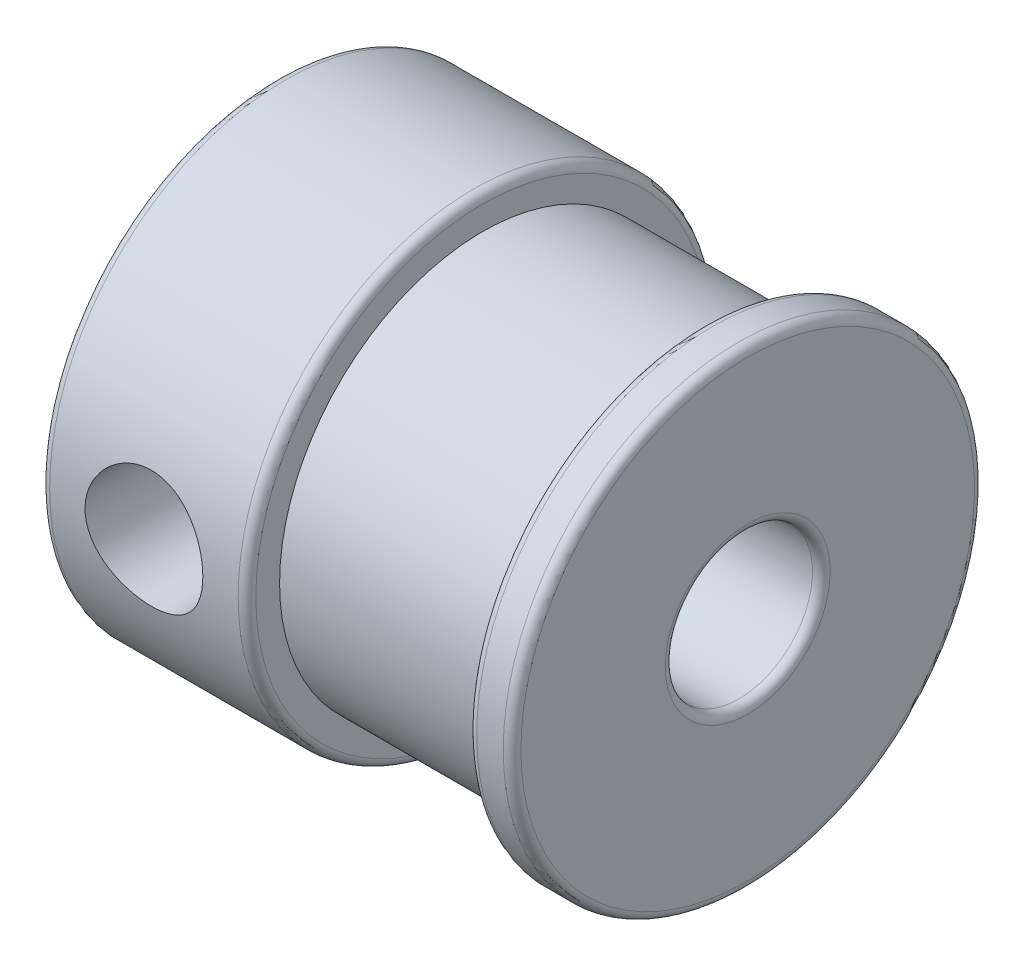
SolidWorks part; units mm, degrees
ref_plane "Front Plane" through (0, 0, 0) normal (0, 0, 1) x (1, 0, 0)
ref_plane "Top Plane" through (0, 0, 0) normal (0, 1, 0) x (1, 0, 0)
ref_plane "Right Plane" through (0, 0, 0) normal (1, 0, 0) x (0, 0, -1)
sketch "Sketch1" plane through (0, 0, 0) normal (0, 1, 0) x (1, 0, 0)
  line L0 (0, 0) -> (0, 2.5) construction
  line L1 (0, 2.5) -> (0, 8)
  line L2 (0, 8) -> (7, 8)
  line L3 (7, 8) -> (7, 6.8938)
  line L4 (7, 6.8938) -> (14.5, 6.8938)
  line L5 (14.5, 6.8938) -> (14.5, 8)
  line L6 (14.5, 8) -> (16, 8)
  line L7 (16, 8) -> (16, 2.5)
  line L8 (16, 2.5) -> (0, 2.5)
  line L9 (0, 0) -> (19.664, 0) construction
  dimension "D1" = 16
  dimension "2.5" = 2.5
  dimension "D2" = 8
  dimension "D3" = 1.5
  dimension "D4" = 7.5
  dimension "D5" = 7
revolve "Revolve1" add sketch "Sketch1" angle 360 about L9
fillet "Fillet1" radius 0.3 6 edges at (7, 0, 8) (0, 0, 8) (16, 0, 8) (14.5, 0, 8) (0, 0, 2.5) (16, 0, 2.5)
sketch "Sketch2" plane through (0, 0, 0) normal (0, 0, 1) x (1, 0, 0)
  line L0 (0, 0) -> (7, 0) construction
  line L1 (7, -6.8938) -> (7, 6.8938) construction
  circle A0 centre (3.5, 0) radius 2
  dimension "D1" = 4
extrude "Cut-Extrude1" cut sketch "Sketch2" against normal through all both and the other way through all
